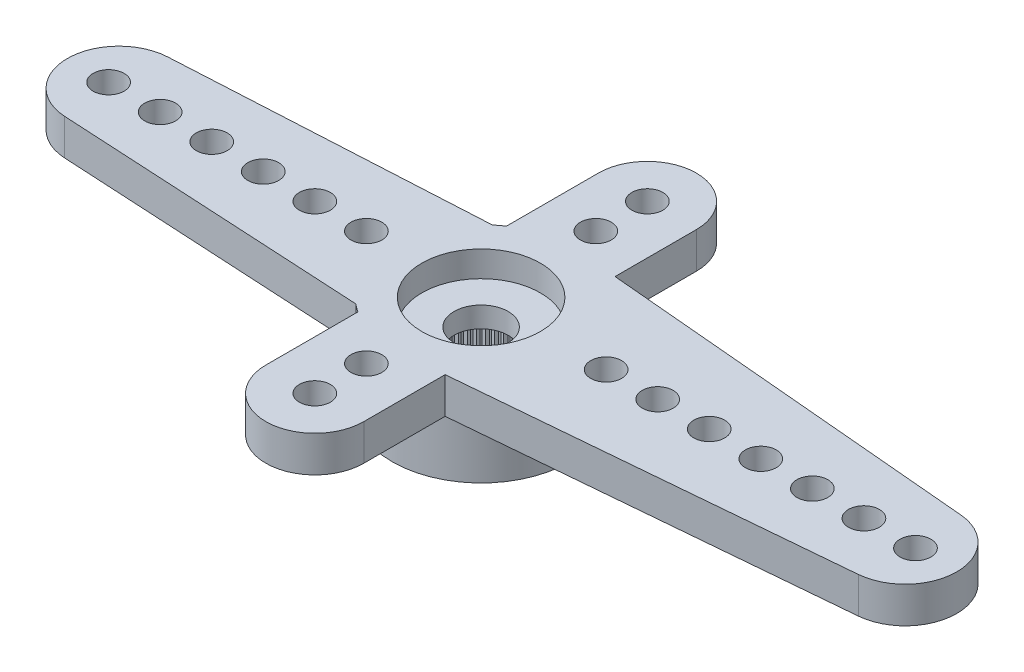
SolidWorks part; units mm, degrees
material "PVC Rígido"
ref_plane "Plano frontal" through (0, 0, 0) normal (0, 0, 1) x (1, 0, 0)
ref_plane "Plano superior" through (0, 0, 0) normal (0, 1, 0) x (1, 0, 0)
ref_plane "Plano direito" through (0, 0, 0) normal (1, 0, 0) x (0, 0, -1)
sketch "Esboço1" plane through (0, 0, 0) normal (0, 1, 0) x (1, 0, 0)
  line L0 (0, 0) -> (-14.05, 0) construction
  line L1 (-14.1591, 1.997) -> (-2.2091, 2.65)
  line L2 (-2.2091, -2.65) -> (-14.1591, -1.997)
  arc A0 (-2.2091, -2.65) -> (-2.2091, 2.65) centre (0, 0) ccw
  arc A1 (-14.1591, 1.997) -> (-14.1591, -1.997) centre (-14.05, 0) ccw
  dimension "D1" = 6.9
  dimension "D2" = 4
  dimension "D3" = 19.5
  dimension "D4" = 5.3
extrude "Ressalto-extrusão1" add sketch "Esboço1" against normal blind 1.4
sketch "Esboço2" plane through (0, -1.4, 0) normal (0, -1, 0) x (1, 0, 0)
  arc A0 (-2.2091, -2.65) -> (-2.2091, 2.65) centre (0, 0) ccw construction
  circle A1 centre (0, 0) radius 3.45
extrude "Ressalto-extrusão2" add sketch "Esboço2" along normal offset from surface (2.4 mm away) 3.8 up to face at (-7.242, 0, 0)
hole_wizard "Furo1" positions "Esboço9" profile "Esboço10" legacy end condition through all
sketch "Esboço9" plane through (0, 0, 0) normal (0, 1, 0) x (1, 0, 0)
  line L1 (-14.45, 0) -> (0, 0) construction
  arc A2 (-14.1591, 1.997) -> (-14.1591, -1.997) centre (-14.05, 0) ccw construction
  point P0 (-14.45, 0)
  point P19 (-16.05, 0)
  dimension "D1" = 1.6
sketch "Esboço10" plane through (-14.45, 0, 0) normal (1, 0, 0) x (0, 0, 1)
  line L0 (0, 0) -> (0, 3.8)
  line L1 (0, 3.8) -> (0.6, 3.8)
  line L2 (0.6, 3.8) -> (0.6, 0)
  line L3 (0.6, 0) -> (0, 0)
  line L4 (0, 110) -> (0, -10) construction
  dimension "Diameter" = 1.2
  dimension "Depth" = 3.8
pattern_linear "Padrão linear1" count 6 spacing 2 along (1, 0, 0) of "Furo1"
sketch "Esboço12" plane through (0, 0, 0) normal (0, 1, 0) x (1, 0, 0)
  line L0 (0.3041, 3.4366) -> (16.6263, 1.9922)
  line L1 (16.6263, -1.9922) -> (0.3041, -3.4366)
  arc A0 (-2.2091, -2.65) -> (-2.2091, 2.65) centre (0, 0) ccw construction
  arc A1 (0.3041, -3.4366) -> (0.3041, 3.4366) centre (0, 0) ccw
  arc A2 (16.6263, 1.9922) -> (16.6263, -1.9922) centre (16.45, 0) cw
  arc A3 (-14.1591, 1.997) -> (-14.1591, -1.997) centre (-14.05, 0) ccw construction
  dimension "D1" = 2
  dimension "D2" = 34.5
extrude "Ressalto-extrusão3" add sketch "Esboço12" against normal up to surface (1.4 mm away) up to face at (-12.45, -1.4, 0.6)
hole_wizard "Furo2" positions "Esboço13" profile "Esboço14" legacy end condition through all
sketch "Esboço13" plane through (0, 0, 0) normal (0, 1, 0) x (1, 0, 0)
  line L0 (0, 0) -> (16.85, 0) construction
  arc A0 (16.6263, -1.9922) -> (16.6263, 1.9922) centre (16.45, 0) ccw construction
  point P0 (16.85, 0)
  point P6 (18.45, 0)
  dimension "D1" = 1.6
sketch "Esboço14" plane through (16.85, 0, 0) normal (1, 0, 0) x (0, 0, 1)
  line L0 (0, 0) -> (0, 3.8)
  line L1 (0, 3.8) -> (0.6, 3.8)
  line L2 (0.6, 3.8) -> (0.6, 0)
  line L3 (0.6, 0) -> (0, 0)
  line L4 (0, 110) -> (0, -10) construction
  dimension "Diameter" = 1.2
  dimension "Depth" = 3.8
pattern_linear "Padrão linear2" count 7 spacing 2 along (-1, 0, 0) of "Furo2"
sketch "Esboço16" plane through (0, 0, 0) normal (0, 1, 0) x (1, 0, 0)
  line L0 (0, -6.45) -> (0, 6.45) construction
  line L1 (-1.9, -6.45) -> (-1.9, 6.45)
  line L2 (1.9, -6.45) -> (1.9, 6.45)
  arc A0 (-1.9, -6.45) -> (1.9, -6.45) centre (0, -6.45) ccw
  arc A1 (1.9, 6.45) -> (-1.9, 6.45) centre (0, 6.45) ccw
  point P2 (0, 0)
  dimension "D2" = 16.7
  dimension "D1" = 3.8
extrude "Ressalto-extrusão4" add sketch "Esboço16" against normal up to surface (1.4 mm away) up to face at (14.85, -1.4, 0.6)
hole_wizard "Furo3" positions "Esboço17" profile "Esboço18" legacy end condition through all
sketch "Esboço17" plane through (0, 0, 0) normal (0, 1, 0) x (1, 0, 0)
  point P0 (0, -6.45)
sketch "Esboço18" plane through (0, 0, 6.45) normal (1, 0, 0) x (0, 0, 1)
  line L0 (0, 0) -> (0, 3.8)
  line L1 (0, 3.8) -> (0.6, 3.8)
  line L2 (0.6, 3.8) -> (0.6, 0)
  line L3 (0.6, 0) -> (0, 0)
  line L4 (0, 110) -> (0, -10) construction
  dimension "Diameter" = 1.2
  dimension "Depth" = 3.8
pattern_linear "Padrão linear3" count 2 spacing 2 along (0, 0, -1) of "Furo3"
pattern_circular "PadrãoCircular1" count 2 over 360 about axis through (0, 0, 0) along (0, 1, 0) of "Padrão linear3", "Furo3"
hole_wizard "Furo4" positions "Esboço3" profile "Esboço4" legacy
sketch "Esboço3" plane through (0, -3.8, 0) normal (0, -1, 0) x (-1, 0, 0)
  point P0 (0, 0)
sketch "Esboço4" plane through (0, -3.8, 0) normal (1, 0, 0) x (0, 0, -1)
  line L0 (0, 0) -> (0, 2)
  line L1 (0, 2) -> (2.475, 2)
  line L2 (2.475, 2) -> (2.475, 0)
  line L3 (2.475, 0) -> (0, 0)
  line L4 (0, 110) -> (0, -10) construction
  dimension "Diameter" = 4.95
  dimension "Depth" = 2
hole_wizard "Furo5" positions "Esboço5" profile "Esboço6" legacy
sketch "Esboço5" plane through (0, 0, 0) normal (0, 1, 0) x (1, 0, 0)
  point P0 (0, 0)
sketch "Esboço6" plane through (0, 0, 0) normal (1, 0, 0) x (0, 0, 1)
  line L0 (0, 0) -> (0, 1)
  line L1 (0, 1) -> (2.3, 1)
  line L2 (2.3, 1) -> (2.3, 0)
  line L3 (2.3, 0) -> (0, 0)
  line L4 (0, 110) -> (0, -10) construction
  dimension "Diameter" = 4.6
  dimension "Depth" = 1
hole_wizard "Furo6" positions "Esboço7" profile "Esboço8" legacy end condition through all
sketch "Esboço7" plane through (0, 0, 0) normal (0, 1, 0) x (1, 0, 0)
  point P0 (0, 0)
sketch "Esboço8" plane through (0, 0, 0) normal (1, 0, 0) x (0, 0, 1)
  line L0 (0, 0) -> (0, 3.8)
  line L1 (0, 3.8) -> (1.05, 3.8)
  line L2 (1.05, 3.8) -> (1.05, 0)
  line L3 (1.05, 0) -> (0, 0)
  line L4 (0, 110) -> (0, -10) construction
  dimension "Diameter" = 2.1
  dimension "Depth" = 3.8
sketch "Esboço11" plane through (0, -3.8, 0) normal (0, -1, 0) x (1, 0, 0)
  line L0 (-0.0981, 2.4731) -> (0, 2.375)
  line L1 (0, 2.375) -> (0.0981, 2.4731)
  line L2 (0, 0) -> (0, 2.475) construction
  circle A0 centre (0, 0) radius 2.375 construction
  circle A1 centre (0, 0) radius 2.475
  arc A2 (0.0981, 2.4731) -> (-0.0981, 2.4731) centre (0, 0) ccw
  dimension "D3" = 4.75
  dimension "D2" = 0.1
  dimension "D1" = 0
extrude "Ressalto-extrusão5" add sketch "Esboço11" against normal up to surface (2 mm away) up to face at (0, -1.8, 1.05)
pattern_circular "PadrãoCircular2" count 60 over 360 about axis through (0, 0, 0) along (0, 1, 0) of "Ressalto-extrusão5"
sketch "Sketch1" [suppressed] plane through (0, 0, 0) normal (0, 1, 0) x (1, 0, 0)
  line L0 (-8.45, 0) -> (8.85, 0) construction
  circle A0 centre (0, 0) radius 1.05
  circle A1 centre (0, 0) radius 2.3
  circle A2 centre (4.85, 0) radius 0.6
  circle A3 centre (6.85, 0) radius 0.6
  circle A4 centre (8.85, 0) radius 0.6
  circle A5 centre (-4.45, 0) radius 0.6
  circle A6 centre (-6.45, 0) radius 0.6
  circle A7 centre (-8.45, 0) radius 0.6
sketch "Sketch2" plane through (-1.9, 0, 0) normal (-1, 0, 0) x (0, 0, 1)
  line L0 (2.8797, 0) -> (2.8797, -3.8015)
